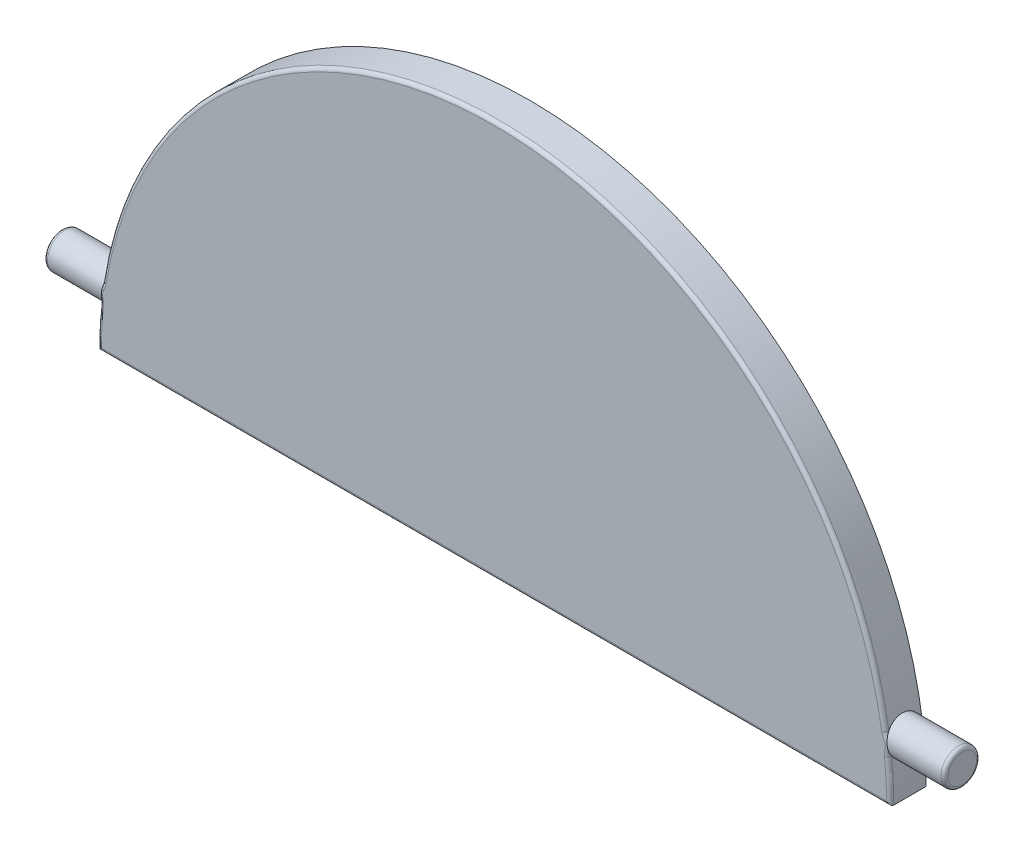
SolidWorks part; units mm, degrees
material "C (Graphite)"
ref_plane "Front Plane" through (0, 0, 0) normal (0, 0, 1) x (1, 0, 0)
ref_plane "Top Plane" through (0, 0, 0) normal (0, 1, 0) x (1, 0, 0)
ref_plane "Right Plane" through (0, 0, 0) normal (1, 0, 0) x (0, 0, -1)
sketch "Sketch1" plane through (0, 0, 0) normal (0, 0, 1) x (1, 0, 0)
  line L0 (11.0035, 0) -> (-10.9965, 0) construction
  line L1 (-10.9965, 0) -> (-10.9965, -11) construction
  line L6 (-10.9965, -11) -> (11.0035, -10.993)
  arc A0 (-10.9965, -11) -> (11.0035, -10.993) centre (0.0035, -11) cw
  dimension "D3" = 22
  dimension "D1" = 11
  dimension "D2" = 22
extrude "Boss-Extrude1" add sketch "Sketch1" along normal blind 1
ref_plane "Plane1" through (0, 0, 0) normal (0, 1, 0) x (1, 0, 0)
sketch "Sketch2" plane through (0, 0, 0) normal (1, 0, 0) x (0, 0, -1)
  circle A0 centre (-0.4952, -9.56) radius 0.495
  dimension "D1" = 0.99
extrude "Boss-Extrude2" add sketch "Sketch2" along normal mid plane 25
fillet "Fillet1" radius 0.1 2 edges at (12.5, -9.56, 0.0002) (-12.5, -9.56, 0.0002)
fillet "Fillet7" radius 0.1 2 edges at (0, 0, 1) (0.0035, -10.9965, 1)
